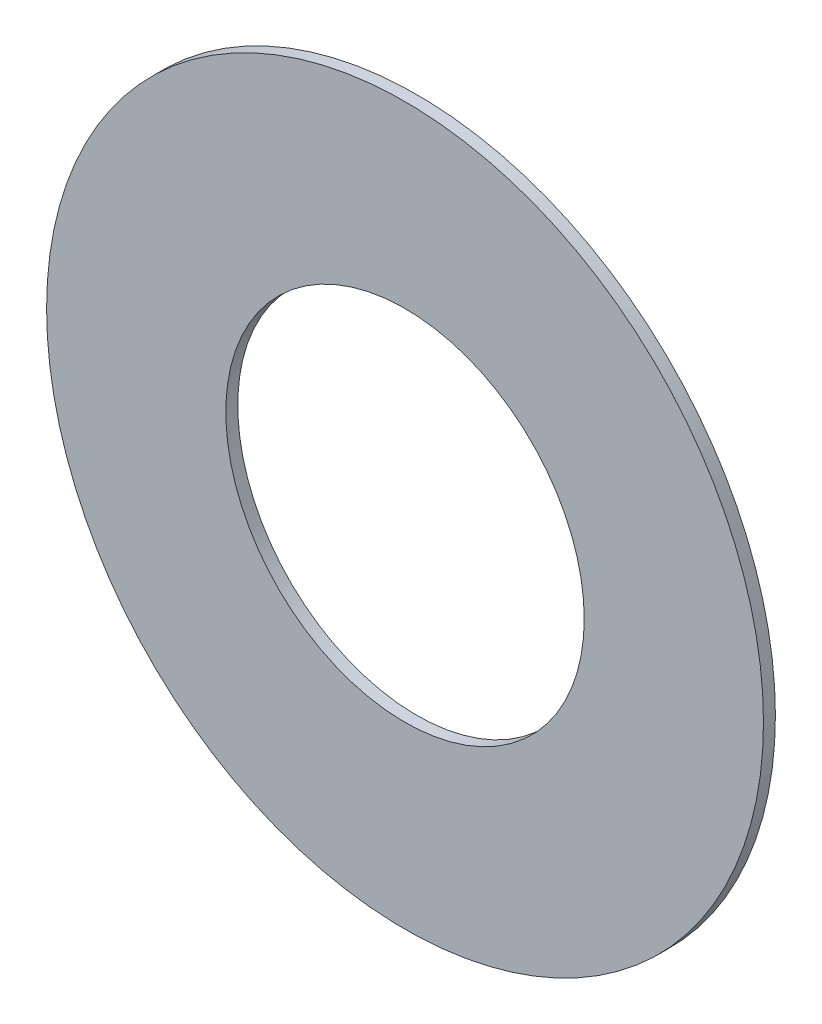
SolidWorks part; units mm, degrees
ref_plane "Front" through (0, 0, 0) normal (0, 0, 1) x (1, 0, 0)
ref_plane "Top" through (0, 0, 0) normal (0, 1, 0) x (1, 0, 0)
ref_plane "Right" through (0, 0, 0) normal (1, 0, 0) x (0, 0, -1)
sketch "Sketch1" plane through (0, 0, 0) normal (0, 0, 1) x (1, 0, 0)
  circle A0 centre (0, 0) radius 3
  circle A1 centre (0, 0) radius 1.5
  dimension "D1" = 3
  dimension "D2" = 6
extrude "Boss-Extrude1" add sketch "Sketch1" along normal blind 0.1
